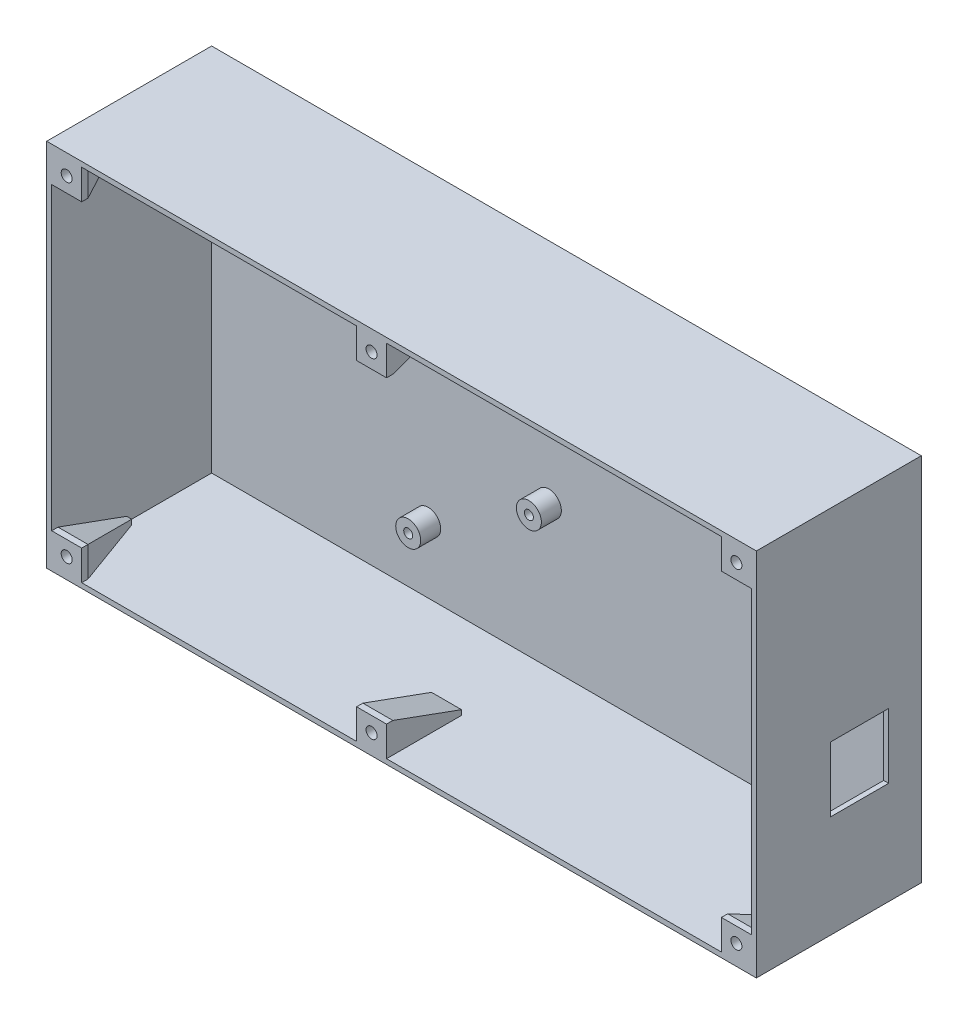
SolidWorks part; units mm, degrees
ref_plane "Plan de face" through (0, 0, 0) normal (0, 0, 1) x (1, 0, 0)
ref_plane "Plan de dessus" through (0, 0, 0) normal (0, 1, 0) x (1, 0, 0)
ref_plane "Plan de droite" through (0, 0, 0) normal (1, 0, 0) x (0, 0, -1)
sketch "Esquisse1" plane through (0, 0, 0) normal (0, 0, 1) x (1, 0, 0)
  line L1 (0, 0) -> (142, 0)
  line L2 (0, 0) -> (0, 74)
  line L3 (0, 74) -> (142, 74)
  line L4 (142, 0) -> (142, 74)
  dimension "D1" = 74
  dimension "D2" = 142
extrude "Boss.-Extru.1" add sketch "Esquisse1" along normal blind 1
sketch "Esquisse2" plane through (0, 0, 1) normal (0, 0, 1) x (1, 0, 0)
  line L1 (0, 74) -> (142, 74)
  line L2 (0, 74) -> (0, 0)
  line L3 (0, 0) -> (142, 0)
  line L4 (142, 74) -> (142, 0)
  line L5 (1, 73) -> (141, 73)
  line L6 (1, 73) -> (1, 1)
  line L7 (1, 1) -> (141, 1)
  line L8 (141, 73) -> (141, 1)
  dimension "D1" = 1
  dimension "D2" = 1
  dimension "D3" = 1
  dimension "D4" = 1
extrude "Boss.-Extru.2" add sketch "Esquisse2" along normal blind 32
sketch "Esquisse3" plane through (0, 0, 33) normal (0, 0, 1) x (1, 0, 0)
  line L0 (1, 1) -> (141, 1) construction
  line L1 (1, 73) -> (7, 73)
  line L2 (1, 73) -> (1, 67)
  line L3 (1, 67) -> (7, 67)
  line L4 (7, 73) -> (7, 67)
  line L5 (141, 73) -> (135, 73)
  line L6 (141, 73) -> (141, 67)
  line L7 (141, 67) -> (135, 67)
  line L8 (135, 73) -> (135, 67)
  line L9 (141, 1) -> (135, 1)
  line L10 (141, 1) -> (141, 7)
  line L11 (141, 7) -> (135, 7)
  line L12 (135, 1) -> (135, 7)
  line L13 (1, 1) -> (7, 1)
  line L14 (1, 1) -> (1, 7)
  line L15 (1, 7) -> (7, 7)
  line L16 (7, 1) -> (7, 7)
  line L17 (62, 1) -> (68, 1)
  line L18 (62, 1) -> (62, 7)
  line L19 (62, 7) -> (68, 7)
  line L20 (68, 1) -> (68, 7)
  line L21 (141, 73) -> (1, 73) construction
  line L22 (62, 73) -> (68, 73)
  line L23 (62, 73) -> (62, 67)
  line L24 (62, 67) -> (68, 67)
  line L25 (68, 73) -> (68, 67)
  dimension "D3" = 6
  dimension "D8" = 6
  dimension "D1" = 6
  dimension "D2" = 6
  dimension "D4" = 6
  dimension "D5" = 6
  dimension "D6" = 6
  dimension "D7" = 6
  dimension "D9" = 6
  dimension "D10" = 6
  dimension "D11" = 6
  dimension "D12" = 6
  dimension "D13" = 55
  dimension "D14" = 67
  dimension "D15" = 55
  dimension "D16" = 67
extrude "Boss.-Extru.3" add sketch "Esquisse3" against normal blind 15
chamfer "Chanfrein1" distance 5 angle 70 10 edges at (7, 4, 18) (4, 7, 18) (65, 7, 18) (135, 4, 18) (138, 7, 18) (135, 70, 18) (138, 67, 18) (65, 67, 18) (7, 70, 18) (4, 67, 18)
sketch "Esquisse4" plane through (0, 0, 33) normal (0, 0, 1) x (1, 0, 0)
  line L0 (7, 67) -> (7, 73) construction
  line L1 (1, 67) -> (7, 67) construction
  line L2 (62, 73) -> (62, 67) construction
  line L3 (62, 67) -> (68, 67) construction
  line L4 (135, 73) -> (135, 67) construction
  line L5 (135, 67) -> (141, 67) construction
  line L6 (135, 7) -> (135, 1) construction
  line L7 (141, 7) -> (135, 7) construction
  line L8 (7, 7) -> (1, 7) construction
  line L9 (7, 1) -> (7, 7) construction
  circle A0 centre (4, 70) radius 1.1
  circle A1 centre (65, 70) radius 1.1
  circle A2 centre (138, 70) radius 1.1
  circle A3 centre (138, 4) radius 1.1
  circle A4 centre (65, 4) radius 1.1
  circle A5 centre (4, 4) radius 1.1
  dimension "D1" = 2.2
  dimension "D4" = 2.2
  dimension "D11" = 2.2
  dimension "D12" = 2.2
  dimension "D13" = 2.2
  dimension "D16" = 2.2
  dimension "D2" = 3
  dimension "D3" = 3
  dimension "D5" = 3
  dimension "D6" = 3
  dimension "D7" = 3
  dimension "D8" = 3
  dimension "D9" = 3
  dimension "D10" = 3
  dimension "D14" = 3
  dimension "D15" = 3
extrude "Enlèv. mat.-Extru.1" cut sketch "Esquisse4" against normal blind 4
sketch "Esquisse5" plane through (0, 0, 1) normal (0, 0, 1) x (1, 0, 0)
  line L2 (62, 73) -> (7, 73) construction
  line L4 (142, 0) -> (142, 74) construction
  circle A0 centre (38, 62.5) radius 0.9
  circle A1 centre (38, 62.5) radius 2.5
  circle A2 centre (68.48, 57.42) radius 0.9
  circle A3 centre (68.48, 57.42) radius 2.5
  circle A4 centre (68.48, 29.48) radius 0.9
  circle A5 centre (68.48, 29.48) radius 2.5
  circle A6 centre (44.3362, 14.2334) radius 0.9
  circle A7 centre (44.3362, 14.2334) radius 2.5
  circle A8 centre (120.551, 62.5) radius 0.9
  circle A9 centre (120.551, 62.5) radius 2.5
  circle A10 centre (119.28, 14.24) radius 0.9
  circle A11 centre (119.28, 14.24) radius 2.5
  dimension "D1" = 1.8
  dimension "D2" = 5
  dimension "D3" = 1.8
  dimension "D4" = 5
  dimension "D5" = 1.8
  dimension "D6" = 5
  dimension "D7" = 1.8
  dimension "D8" = 5
  dimension "D9" = 1.8
  dimension "D10" = 5
  dimension "D11" = 1.8
  dimension "D12" = 5
  dimension "D13" = 30.48
  dimension "D14" = 5.08
  dimension "D15" = 27.94
  dimension "D16" = 30.48
  dimension "D17" = 24.1438
  dimension "D18" = 15.2466
  dimension "D19" = 50.8
  dimension "D20" = 15.24
  dimension "D21" = 52.071
  dimension "D22" = 5.08
  dimension "D23" = 10.5
  dimension "D24" = 104
extrude "Boss.-Extru.4" add sketch "Esquisse5" along normal blind 4
sketch "Esquisse6" plane through (142, 0, 0) normal (1, 0, 0) x (0, 0, -1)
  line L0 (-33, 0) -> (0, 0) construction
  line L1 (-18.1685, 20.5) -> (-6.5327, 20.5)
  line L2 (-18.1685, 20.5) -> (-18.1685, 33.4771)
  line L3 (-18.1685, 33.4771) -> (-6.5327, 33.4771)
  line L4 (-6.5327, 20.5) -> (-6.5327, 33.4771)
  dimension "D1" = 12.9771
  dimension "D2" = 11.6359
  dimension "D3" = 20.5
extrude "Enlèv. mat.-Extru.2" cut sketch "Esquisse6" against normal blind 3
